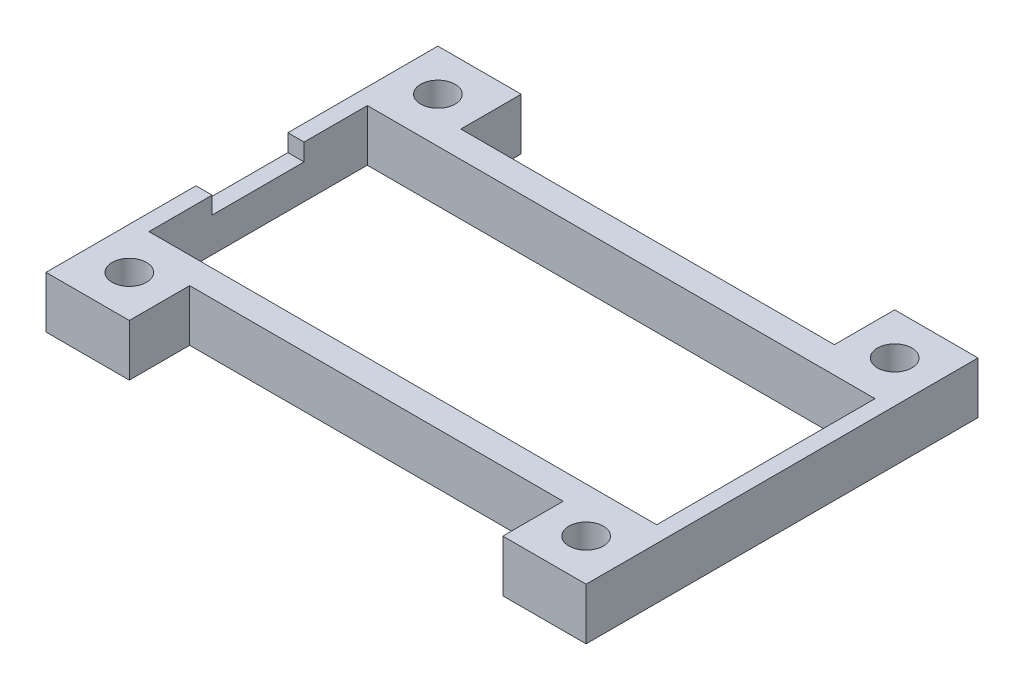
SolidWorks part; units mm, degrees
ref_plane "Front Plane" through (0, 0, 0) normal (0, 0, 1) x (1, 0, 0)
ref_plane "Top Plane" through (0, 0, 0) normal (0, 1, 0) x (1, 0, 0)
ref_plane "Right Plane" through (0, 0, 0) normal (1, 0, 0) x (0, 0, -1)
sketch "Sketch1" plane through (0, 0, 0) normal (0, 1, 0) x (1, 0, 0)
  line L1 (0, 0) -> (44.18, 0)
  line L2 (0, 0) -> (0, 19)
  line L3 (0, 19) -> (44.18, 19)
  line L4 (44.18, 0) -> (44.18, 19)
  line L5 (-1.41, 21.3) -> (45.59, 21.3)
  line L6 (-1.41, 21.3) -> (-1.41, -2.3)
  line L7 (-1.41, -2.3) -> (45.59, -2.3)
  line L8 (45.59, 21.3) -> (45.59, -2.3)
  point P9 (22.09, 21.3)
  point P10 (22.09, 19)
  point P11 (0, 9.5)
  point P12 (-1.41, 9.5)
  point P13 (22.09, 19)
  dimension "D1" = 19
  dimension "D2" = 44.18
  dimension "D3" = 47
  dimension "D4" = 23.6
extrude "Boss-Extrude1" add sketch "Sketch1" along normal blind 4.5
sketch "Sketch6" plane through (0, 0, 2.3) normal (0, 0, 1) x (1, 0, 0)
  line L0 (-1.41, 0) -> (45.59, 0) construction
  line L1 (-1.41, 4.5) -> (5.84, 4.5)
  line L2 (-1.41, 4.5) -> (-1.41, 0)
  line L3 (-1.41, 0) -> (5.84, 0)
  line L4 (5.84, 4.5) -> (5.84, 0)
  line L6 (45.59, 4.5) -> (38.34, 4.5)
  line L7 (45.59, 4.5) -> (45.59, 0)
  line L8 (45.59, 0) -> (38.34, 0)
  line L9 (38.34, 4.5) -> (38.34, 0)
  dimension "D1" = 7.25
  dimension "D2" = 7.25
extrude "Boss-Extrude3" add sketch "Sketch6" along normal blind 5.25
sketch "Sketch7" plane through (0, 0, -21.3) normal (0, 0, -1) x (-1, 0, 0)
  line L0 (-45.59, 0) -> (1.41, 0) construction
  line L1 (-45.59, 4.5) -> (-38.34, 4.5)
  line L2 (-45.59, 4.5) -> (-45.59, 0)
  line L3 (-45.59, 0) -> (-38.34, 0)
  line L4 (-38.34, 4.5) -> (-38.34, 0)
  line L6 (1.41, 4.5) -> (-5.84, 4.5)
  line L7 (1.41, 4.5) -> (1.41, 0)
  line L8 (1.41, 0) -> (-5.84, 0)
  line L9 (-5.84, 4.5) -> (-5.84, 0)
  dimension "D1" = 7.25
  dimension "D2" = 7.25
extrude "Boss-Extrude4" add sketch "Sketch7" along normal blind 5.25
sketch "Sketch8" plane through (0, 4.5, 0) normal (0, 1, 0) x (1, 0, 0)
  line L0 (45.59, -7.55) -> (45.59, 26.55) construction
  line L1 (38.34, 26.55) -> (45.59, 26.55) construction
  line L2 (44.18, 9.5) -> (-13.9525, 9.5) construction
  line L3 (44.18, 0) -> (44.18, 19) construction
  line L4 (22.09, 0) -> (22.09, 19) construction
  line L5 (0, 0) -> (44.18, 0) construction
  line L6 (44.18, 19) -> (0, 19) construction
  circle A0 centre (41.965, 22.925) radius 1.5
  circle A1 centre (41.965, -3.925) radius 1.5
  circle A2 centre (2.215, -3.925) radius 1.5
  circle A3 centre (2.215, 22.925) radius 1.5
  point P4 (41.965, 26.55)
  dimension "D1" = 3
  dimension "D2" = 3.625
  dimension "D3" = 3.625
extrude "Cut-Extrude2" cut sketch "Sketch8" against normal through all
sketch "Sketch10" plane through (0, 4.5, 0) normal (0, 1, 0) x (1, 0, 0)
  line L0 (-1.41, 26.55) -> (-1.41, -7.55) construction
  line L1 (-1.41, 13.5) -> (0, 13.5)
  line L2 (-1.41, 13.5) -> (-1.41, 5.5)
  line L3 (-1.41, 5.5) -> (0, 5.5)
  line L4 (0, 13.5) -> (0, 5.5)
  line L5 (0, 19) -> (0, 0) construction
  line L7 (44.18, 0) -> (44.18, 19) construction
  point P9 (44.18, 9.5)
  point P10 (0, 9.5)
  dimension "D1" = 8
extrude "Cut-Extrude3" cut sketch "Sketch10" against normal blind 1.5
